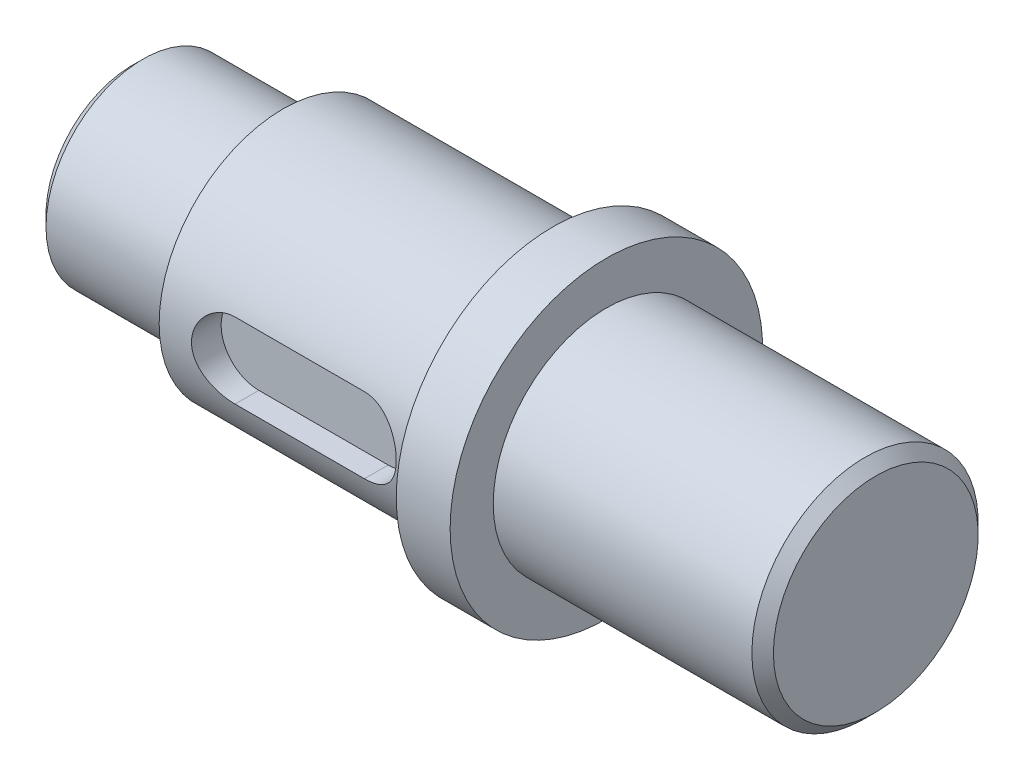
SolidWorks part; units mm, degrees
ref_plane "Front Plane" through (0, 0, 0) normal (0, 0, 1) x (1, 0, 0)
ref_plane "Top Plane" through (0, 0, 0) normal (0, 1, 0) x (1, 0, 0)
ref_plane "Right Plane" through (0, 0, 0) normal (1, 0, 0) x (0, 0, -1)
sketch "Sketch1" plane through (0, 0, 0) normal (0, 0, 1) x (1, 0, 0)
  line L0 (0, 0) -> (138, 0) construction
  line L1 (0, 0) -> (0, 18)
  line L2 (0, 18) -> (28, 18)
  line L3 (28, 18) -> (28, 23)
  line L4 (28, 23) -> (78, 23)
  line L5 (78, 23) -> (78, 29)
  line L6 (78, 29) -> (88, 29)
  line L7 (88, 29) -> (88, 21)
  line L8 (88, 21) -> (138, 21)
  line L9 (138, 21) -> (138, 0)
  line L10 (0, 0) -> (138, 0)
  dimension "D1" = 28
  dimension "D2" = 50
  dimension "D3" = 10
  dimension "D4" = 50
  dimension "D5" = 36
  dimension "D6" = 46
  dimension "D7" = 58
  dimension "D8" = 42
revolve "Revolve1" add sketch "Sketch1" angle 360 about L0
cosmetic thread "Cosmetic Thread1" parameters "D1"=25, "D2"=31.61
ref_plane "Plane1" through (0, 0, 23) normal (0, 0, 1) x (1, 0, 0)
sketch "Sketch2" plane through (0, 0, 23) normal (0, 0, 1) x (1, 0, 0)
  line L0 (41, 0) -> (65, 0) construction
  line L1 (41, 7) -> (65, 7)
  line L2 (41, -7) -> (65, -7)
  line L3 (78, 23) -> (78, -23) construction
  arc A0 (41, 7) -> (41, -7) centre (41, 0) ccw
  arc A1 (65, -7) -> (65, 7) centre (65, 0) ccw
  point P3 (53, 0)
  dimension "D1" = 24
  dimension "D2" = 13
  dimension "D3" = 14
extrude "Cut-Extrude1" cut sketch "Sketch2" against normal blind 5.5
chamfer "Chamfer2" distance 2 angle 45 2 edges at (138, 0, 21) (0, 0, 18)
cosmetic thread "Cosmetic Thread2" parameters "D2"=31.61
